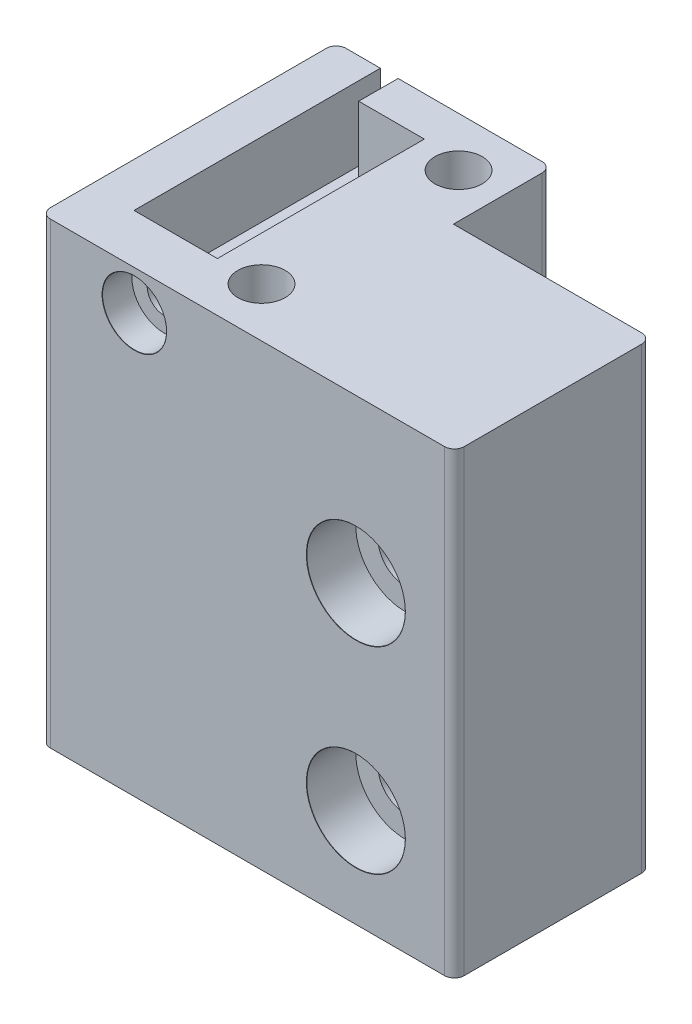
SolidWorks part; units mm, degrees
ref_plane "Front Plane" through (0, 0, 0) normal (0, 0, 1) x (1, 0, 0)
ref_plane "Top Plane" through (0, 0, 0) normal (0, 1, 0) x (1, 0, 0)
ref_plane "Right Plane" through (0, 0, 0) normal (1, 0, 0) x (0, 0, -1)
sketch "Sketch1" plane through (0, 0, 0) normal (0, 1, 0) x (1, 0, 0)
  line L1 (21, 10) -> (-21, 10)
  line L2 (21, 10) -> (21, -10)
  line L3 (21, -10) -> (-21, -10)
  line L4 (-21, 10) -> (-21, -10)
  line L5 (21, 10) -> (-21, -10) construction
  line L6 (21, -10) -> (-21, 10) construction
  point P0 (0, 0)
  dimension "D1" = 20
  dimension "D2" = 42
extrude "Boss-Extrude1" add sketch "Sketch1" along normal blind 40
sketch "Sketch2" plane through (0, 0, 10) normal (0, 0, 1) x (1, 0, 0)
  line L0 (21, 20) -> (-21, 20) construction
  line L3 (21, 40) -> (21, 0) construction
  line L4 (-21, 40) -> (-21, 0) construction
  line L5 (11, 30) -> (11, 10)
  point P9 (11, 20)
  dimension "D1" = 20
  dimension "D2" = 10
hole_wizard "CBORE for M5 SHCS1" positions "Sketch3" profile "Sketch4" counterbore size "M5" standard "ANSI Metric" end condition through all
sketch "Sketch3" plane through (0, 0, 10) normal (0, 0, 1) x (1, 0, 0)
  point P0 (11, 30)
  point P3 (11, 10)
sketch "Sketch4" plane through (11, 30, 10) normal (1, 0, 0) x (0, -1, 0)
  line L0 (0, 0) -> (0, 20)
  line L1 (0, 20) -> (2.75, 20)
  line L3 (2.75, 20) -> (2.75, 5)
  line L4 (5, 5) -> (2.75, 5)
  line L5 (5, 5) -> (5, 0.021)
  line L6 (5, 0.021) -> (5.025, 0)
  line L7 (5.025, 0) -> (0, 0)
  line L8 (-5, 0.021) -> (-5.025, 0) construction
  line L11 (0, -6.35) -> (0, 107.95) construction
  dimension "Thru Hole Dia." = 5.5
  dimension "Thru Hole Depth" = 20
  dimension "C'Bore Dia." = 10
  dimension "C'Bore Depth" = 5
  dimension "Near C'Sink Dia." = 10.05
  dimension "Near C'Sink Angle" = 100
sketch "Sketch5" plane through (0, 40, 0) normal (0, 1, 0) x (1, 0, 0)
  line L4 (-21, 10) -> (-21, -10)
  line L5 (-21, -10) -> (21, -10)
  line L6 (21, -10) -> (21, 10)
  line L7 (21, 10) -> (-21, 10)
  line L8 (-21, 10) -> (-21, -10)
  line L9 (-21, -10) -> (21, -10)
  line L10 (21, -10) -> (21, 10)
  line L11 (21, 10) -> (-21, 10)
  dimension "D1" = 0
extrude "Boss-Extrude2" add sketch "Sketch5" along normal blind 6.5
sketch "Sketch12" plane through (0, 46.5, 0) normal (0, 1, 0) x (1, 0, 0)
  line L0 (21, -10) -> (21, 10) construction
  line L1 (-21, 10) -> (0.9, 10)
  line L2 (-21, 10) -> (-21, 20)
  line L3 (-21, 20) -> (0.9, 20)
  line L4 (0.9, 10) -> (0.9, 20)
  dimension "D1" = 10
  dimension "D2" = 20.1
extrude "Boss-Extrude3" add sketch "Sketch12" against normal up to surface (46.5 mm away) up to face at (0, 0, 0)
sketch "Sketch6" plane through (0, 46.5, 0) normal (0, 1, 0) x (1, 0, 0)
  line L0 (-16.51, 20) -> (-16.51, -5)
  line L2 (-16.51, -5) -> (-8.05, -5)
  line L3 (-8.05, -5) -> (-8.05, 16)
  line L4 (-8.05, 16) -> (-14.71, 16)
  line L5 (-14.71, 16) -> (-14.71, 20)
  line L6 (-21, 20) -> (-21, -10) construction
  line L7 (-16.51, 20) -> (-14.71, 20)
  line L8 (21, -10) -> (-21, -10) construction
  line L9 (0.9, 20) -> (-21, 20) construction
  dimension "D1" = 4.49
  dimension "D2" = 1.8
  dimension "D3" = 5
  dimension "D4" = 8.46
  dimension "D5" = 4
extrude "Cut-Extrude1" cut sketch "Sketch6" against normal blind 7.5
fillet "Fillet1" radius 1 5 edges at (0.9, 23.25, -20) (21, 23.25, 10) (-21, 23.25, -20) (-21, 23.25, 10) (21, 23.25, -10)
sketch "Sketch7" plane through (0, 0, 10) normal (0, 0, 1) x (1, 0, 0)
  circle A0 centre (-11.48, 42.5) radius 1.65 construction
  circle A1 centre (-11.48, 42.5) radius 1.65
hole_wizard "CBORE for M3 SHCS1" positions "Sketch10" profile "Sketch11" counterbore size "M3" standard "ANSI Metric"
sketch "Sketch10" plane through (0, 0, 10) normal (0, 0, 1) x (1, 0, 0)
  point P0 (-11.48, 42.5)
sketch "Sketch11" plane through (-11.48, 42.5, 10) normal (1, 0, 0) x (0, -1, 0)
  line L0 (0, 0) -> (0, 6.0215)
  line L1 (0, 6.0215) -> (1.7, 5)
  line L2 (1.7, 5) -> (1.7, 3)
  line L3 (1.7, 3) -> (3.25, 3)
  line L5 (3.25, 3) -> (3.25, 0.021)
  line L6 (3.25, 0.021) -> (3.275, 0)
  line L7 (3.275, 0) -> (0, 0)
  line L8 (-3.25, 0.021) -> (-3.275, 0) construction
  line L10 (0, 6.0215) -> (-1.7, 5) construction
  line L11 (0, -6.35) -> (0, 107.95) construction
  dimension "Hole Dia." = 3.4
  dimension "Hole Depth" = 5
  dimension "C'Bore Dia." = 6.5
  dimension "C'Bore Depth" = 3
  dimension "Near C'Sink Dia." = 6.55
  dimension "Near C'Sink Angle" = 100
  dimension "Drill Angle" = 118
sketch "Sketch14" plane through (0, 46.5, 0) normal (0, 1, 0) x (1, 0, 0)
  line L0 (-3.575, 20) -> (-3.575, -10) construction
  line L1 (-0.1, 20) -> (-14.71, 20) construction
  line L2 (-20, -10) -> (20, -10) construction
  line L3 (0.9, 10) -> (0.9, 19) construction
  line L4 (-3.575, 15) -> (-3.575, -5) construction
  circle A0 centre (-3.575, 15) radius 2.4
  circle A1 centre (-3.575, -5) radius 2.4
  point P12 (-3.575, 5)
  dimension "D3" = 4.8
  dimension "D1" = 4.475
  dimension "D2" = 20
extrude "Cut-Extrude2" cut sketch "Sketch14" against normal blind 3.8
sketch "Sketch15" plane through (0, 42.7, 0) normal (0, 1, 0) x (1, 0, 0)
  circle A0 centre (-3.575, 15) radius 1.7
  circle A1 centre (-3.575, -5) radius 1.7
  point P0 (-3.575, 15)
  point P1 (-3.575, -5)
  dimension "D1" = 3.4
extrude "Cut-Extrude3" cut sketch "Sketch15" against normal blind 3
